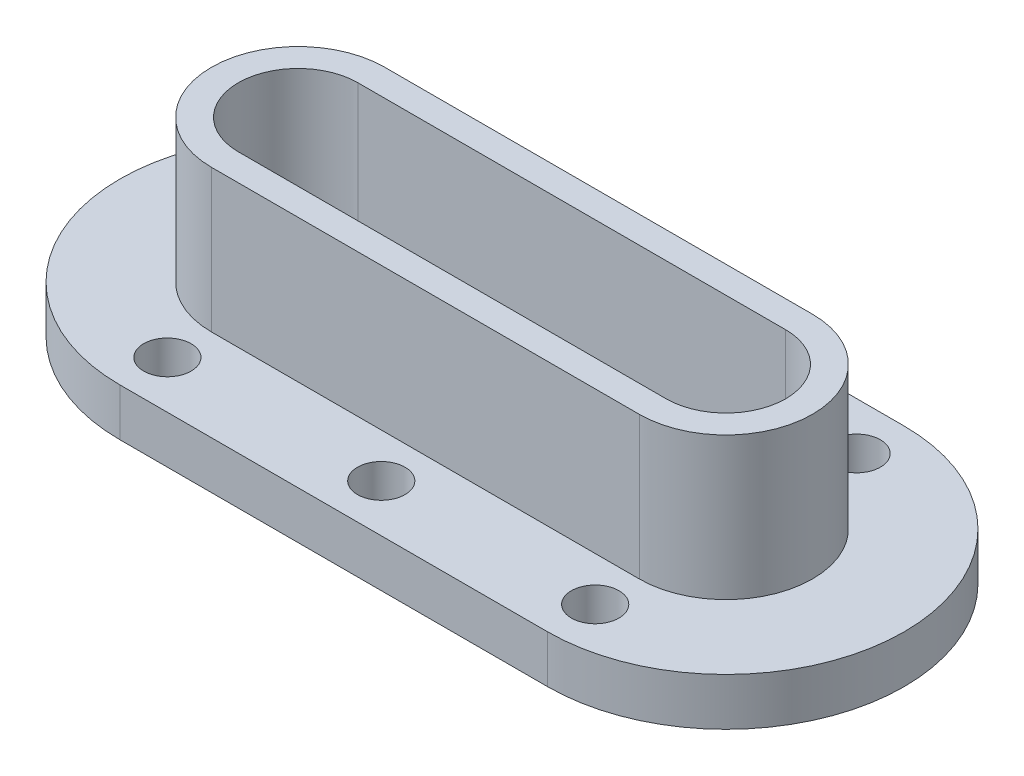
SolidWorks part; units mm, degrees
ref_plane "Front Plane" through (0, 0, 0) normal (0, 0, 1) x (1, 0, 0)
ref_plane "Top Plane" through (0, 0, 0) normal (0, 1, 0) x (1, 0, 0)
ref_plane "Right Plane" through (0, 0, 0) normal (1, 0, 0) x (0, 0, -1)
sketch "Sketch1" plane through (0, 0, 0) normal (0, 1, 0) x (1, 0, 0)
  line L0 (0, 101.8086) -> (0, 75) construction
  line L1 (-188.9097, 0) -> (-165, 0) construction
  line L2 (-90, -75) -> (90, -75)
  line L4 (-90, 75) -> (90, 75)
  line L5 (-90, -75) -> (90, -75) construction
  line L6 (0, -75) -> (0, -109.9794) construction
  arc A0 (-90, 75) -> (-90, -75) centre (-90, 0) ccw
  arc A1 (90, -75) -> (90, 75) centre (90, 0) ccw
  dimension "D4" = 150
  dimension "D1" = 180
extrude "Boss-Extrude1" add sketch "Sketch1" along normal blind 20
sketch "Sketch2" plane through (0, 20, 0) normal (0, 1, 0) x (1, 0, 0)
  line L0 (0, 137.0384) -> (0, -128.4601) construction
  line L1 (-241.4793, 0) -> (247.4841, 0) construction
  line L2 (-90, 137.0384) -> (-90, -128.4601) construction
  line L3 (90, 137.0384) -> (90, -128.4601) construction
  line L4 (-241.4793, -55) -> (247.4841, -55) construction
  line L5 (-241.4793, 55) -> (247.4841, 55) construction
  circle A0 centre (-90, 55) radius 10
  dimension "D5" = 20
  dimension "D1" = 90
  dimension "D2" = 90
  dimension "D3" = 55
  dimension "D4" = 55
extrude "Cut-Extrude1" cut sketch "Sketch2" against normal blind 20
pattern_linear "LPattern1" count 3 spacing 90 along (1, 0, 0) of "Cut-Extrude1"
sketch "Sketch4" plane through (0, 20, 0) normal (0, 1, 0) x (1, 0, 0)
  line L0 (0, 172.8953) -> (0, -176.491) construction
  line L3 (-90, -75) -> (90, -75) construction
  circle A0 centre (-90, -55) radius 10
  dimension "D4" = 20
  dimension "D3" = 20
extrude "Cut-Extrude2" cut sketch "Sketch4" against normal blind 20 contours A0
pattern_linear "LPattern2" count 3 spacing 90 along (1, 0, 0) of "Cut-Extrude2"
sketch "Sketch5" plane through (0, 20, 0) normal (0, 1, 0) x (1, 0, 0)
  line L0 (0, 158.5123) -> (0, -132.1436) construction
  line L1 (-90, 158.5123) -> (-90, -132.1436) construction
  line L2 (90, 158.5123) -> (90, -132.1436) construction
  circle A0 centre (-90, 0) radius 7.5
  dimension "D3" = 15
  dimension "D1" = 90
  dimension "D2" = 90
extrude "Cut-Extrude4" cut sketch "Sketch5" against normal blind 20
pattern_linear "LPattern4" count 3 spacing 90 along (1, 0, 0) of "Cut-Extrude4"
sketch "Sketch6" plane through (0, 20, 0) normal (0, 1, 0) x (1, 0, 0)
  line L0 (0, 134.036) -> (0, -130.1758) construction
  line L1 (-90, 36.4564) -> (90, 36.4564)
  line L2 (-90, -36.4564) -> (90, -36.4564)
  line L3 (-90, 25.1603) -> (90, 25.1603)
  line L4 (-90, -25.1603) -> (90, -25.1603)
  arc A0 (90, -36.4564) -> (90, 36.4564) centre (90, 0) ccw
  arc A1 (90, -25.1603) -> (90, 25.1603) centre (90, 0) ccw
  arc A2 (-90, -25.1603) -> (-90, 25.1603) centre (-90, 0) cw
  arc A3 (-90, -36.4564) -> (-90, 36.4564) centre (-90, 0) cw
extrude "Boss-Extrude3" add sketch "Sketch6" along normal blind 60
